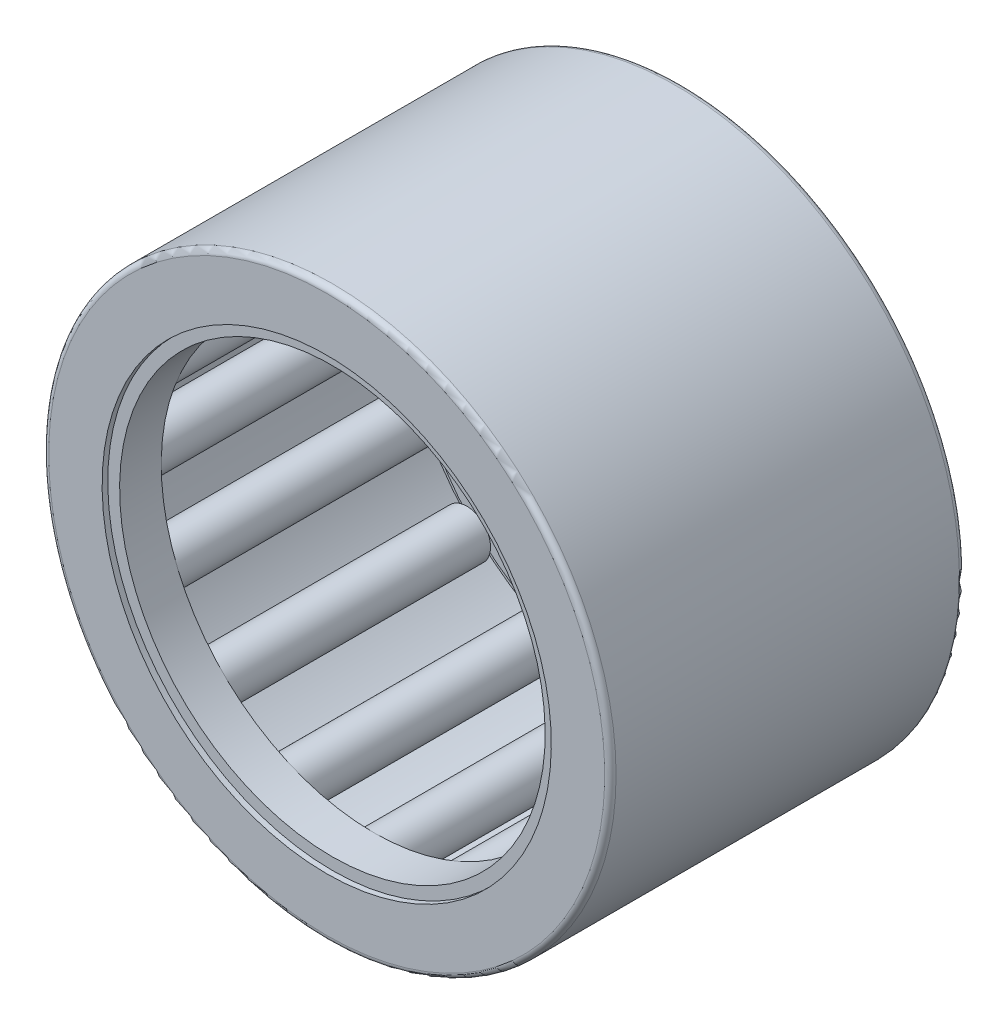
SolidWorks part; units mm, degrees
material "Alloy Steel"
ref_plane "Front Plane" through (0, 0, 0) normal (0, 0, 1) x (1, 0, 0)
ref_plane "Top Plane" through (0, 0, 0) normal (0, 1, 0) x (1, 0, 0)
ref_plane "Right Plane" through (0, 0, 0) normal (1, 0, 0) x (0, 0, -1)
sketch "Sketch1" plane through (0, 0, 0) normal (1, 0, 0) x (0, 0, -1)
  line L0 (-7.9375, 0) -> (7.9375, 0) construction
  line L1 (0, 0) -> (0, 12.7) construction
  line L2 (-7.9375, 0) -> (-7.9375, 12.7) construction
  line L3 (-7.9375, 12.7) -> (7.9375, 12.7)
  line L4 (7.9375, 12.7) -> (7.9375, 0) construction
  line L5 (7.9375, 0) -> (6.8792, 0) construction
  line L6 (6.8792, 0) -> (6.8792, 11.6417) construction
  line L7 (6.8792, 11.6417) -> (-6.8792, 11.6417)
  line L8 (-6.8792, 11.6417) -> (-6.8792, 0) construction
  line L9 (-6.8792, 0) -> (-7.9375, 0) construction
  line L10 (-7.9375, 12.7) -> (-7.9375, 10.0542)
  line L11 (-7.9375, 10.0542) -> (-6.8792, 10.0542)
  line L12 (-6.8792, 10.0542) -> (-6.8792, 11.6417)
  line L13 (6.8792, 12.7) -> (6.8792, 11.6417) construction
  line L14 (6.8792, 11.6417) -> (6.8792, 10.0542)
  line L15 (6.8792, 10.0542) -> (7.9375, 10.0542)
  line L16 (7.9375, 10.0542) -> (7.9375, 12.7)
  line L17 (6.8792, 11.6417) -> (6.8792, 10.5833) construction
  line L18 (6.8792, 10.5833) -> (6.8792, 9.525) construction
  line L19 (6.8792, -11.6417) -> (6.8792, -10.5833) construction
  line L20 (6.8792, -12.7) -> (6.8792, -11.6417) construction
  line L21 (7.9375, -10.0542) -> (7.9375, -12.7) construction
  line L22 (6.8792, -10.0542) -> (7.9375, -10.0542) construction
  line L23 (6.8792, -11.6417) -> (6.8792, -10.0542) construction
  line L24 (-6.8792, -10.0542) -> (-6.8792, -11.6417) construction
  line L25 (-7.9375, -10.0542) -> (-6.8792, -10.0542) construction
  line L26 (-7.9375, -12.7) -> (-7.9375, -10.0542) construction
  line L27 (6.8792, -11.6417) -> (-6.8792, -11.6417) construction
  line L28 (-7.9375, -12.7) -> (7.9375, -12.7) construction
  point P5 (0, 9.525)
  dimension "Width" = 15.875
  dimension "OD" = 25.4
  dimension "Shaft Dia" = 19.05
revolve "Revolve1" add sketch "Sketch1" angle 360 about L0
sketch "Sketch2" plane through (0, 0, 0) normal (1, 0, 0) x (0, 0, -1)
  line L0 (6.8792, 11.6417) -> (-6.8792, 11.6417) construction
  line L1 (-5.8208, 10.5833) -> (5.8208, 10.5833) construction
  line L2 (-5.8208, 10.5833) -> (-5.8208, 11.6417) construction
  line L3 (-5.8208, 11.6417) -> (5.8208, 11.6417)
  line L4 (5.8208, 10.5833) -> (5.8208, 11.6417) construction
  line L5 (6.8792, 10.0542) -> (7.9375, 10.0542) construction
  line L6 (-6.8792, 10.5833) -> (-5.8208, 10.5833) construction
  line L7 (5.8208, 10.5833) -> (6.8792, 10.5833) construction
  line L8 (-7.9375, 10.0542) -> (-6.8792, 10.0542) construction
  line L9 (-5.8208, 10.8479) -> (-5.8208, 10.3188) construction
  line L10 (-6.8792, 10.5833) -> (-6.8792, 10.0542) construction
  line L11 (-5.8208, 11.6417) -> (-5.8208, 10.8479)
  line L12 (5.8208, 11.6417) -> (5.8208, 10.8479)
  line L13 (5.8208, 10.8479) -> (-5.8208, 10.8479)
  line L14 (0, 11.6417) -> (0, 9.525) construction
  line L15 (-6.8792, 10.0542) -> (-6.8792, 11.6417) construction
  line L16 (-5.8208, 10.3188) -> (-6.8792, 10.3188) construction
  line L17 (0, 0) -> (7.9375, 0) construction
  line L18 (-5.8208, -10.3188) -> (-6.8792, -10.3188) construction
  line L19 (0, -11.6417) -> (0, -9.525) construction
  line L20 (-6.8792, -10.5833) -> (-6.8792, -10.0542) construction
  line L21 (-5.8208, -10.8479) -> (-5.8208, -10.3188) construction
  line L22 (5.8208, -10.5833) -> (6.8792, -10.5833) construction
  line L23 (-6.8792, -10.5833) -> (-5.8208, -10.5833) construction
  line L24 (5.8208, -10.5833) -> (5.8208, -11.6417) construction
  line L25 (-5.8208, -10.5833) -> (-5.8208, -11.6417) construction
  line L26 (-5.8208, -10.5833) -> (5.8208, -10.5833) construction
  line L27 (5.8208, -10.8479) -> (-5.8208, -10.8479) construction
  line L28 (5.8208, -11.6417) -> (5.8208, -10.8479) construction
  line L29 (-5.8208, -11.6417) -> (-5.8208, -10.8479) construction
  line L30 (-5.8208, -11.6417) -> (5.8208, -11.6417) construction
  line L31 (7.9375, -12.7) -> (7.9375, 12.7) construction
  point P16 (0, 10.5833)
revolve "Revolve2" add sketch "Sketch2" angle 360 about L1
sketch "Sketch3" plane through (0, 0, 0) normal (1, 0, 0) x (0, 0, -1)
  line L0 (6.8792, 11.6417) -> (6.8792, 10.0542) construction
  line L1 (-6.8792, 10.5833) -> (6.8792, 10.5833)
  line L2 (-6.8792, 10.5833) -> (-6.8792, 10.8479)
  line L3 (-6.8792, 10.8479) -> (6.8792, 10.8479)
  line L4 (6.8792, 10.5833) -> (6.8792, 10.8479)
  line L5 (0, 0) -> (7.9375, 0) construction
  line L6 (7.9375, -12.7) -> (7.9375, 12.7) construction
  line L7 (6.8792, -10.5833) -> (6.8792, -10.8479) construction
  line L8 (-6.8792, -10.8479) -> (6.8792, -10.8479) construction
  line L9 (-6.8792, -10.5833) -> (-6.8792, -10.8479) construction
  line L10 (-6.8792, -10.5833) -> (6.8792, -10.5833) construction
revolve "Revolve3" add sketch "Sketch3" angle 360 about L1
ref_axis "Axis1" through (0, 0, -7.9375) along (0, 0, 1)
pattern_circular "CirPattern1" count 16 every 22.5 about axis through (0, 0, -7.9375) along (0, 0, 1) of bodies 166 167
fillet "Fillet1" radius 0.254 2 edges at (0, -12.7, -7.9375) (0, -12.7, 7.9375)
sketch "Sketch4" plane through (0, 0, 0) normal (1, 0, 0) x (0, 0, -1)
  line L1 (7.6835, 9.525) -> (5.8208, 9.525)
  line L2 (7.6835, 9.525) -> (7.6835, 10.0542)
  line L3 (7.6835, 10.0542) -> (5.8208, 10.0542)
  line L4 (5.8208, 9.525) -> (5.8208, 10.0542)
  line L5 (-7.9375, 10.0542) -> (-6.8792, 10.0542) construction
  line L6 (7.6835, -12.7) -> (7.6835, 12.7) construction
  line L7 (5.8208, 11.6417) -> (5.8208, 10.8479) construction
revolve "Revolve4" add sketch "Sketch4" angle 360 about L0
sketch "Sketch5" plane through (0, 0, 0) normal (1, 0, 0) x (0, 0, -1)
  line L0 (-7.6835, 12.7) -> (-7.6835, -12.7) construction
  line L1 (-5.8208, 9.525) -> (-7.6835, 9.525)
  line L2 (-5.8208, 9.525) -> (-5.8208, 10.0542)
  line L3 (-5.8208, 10.0542) -> (-7.6835, 10.0542)
  line L4 (-7.6835, 9.525) -> (-7.6835, 10.0542)
  line L6 (-5.8208, 11.6417) -> (-5.8208, 10.8479) construction
  line L7 (-7.9375, 10.0542) -> (-6.8792, 10.0542) construction
revolve "Revolve5" add sketch "Sketch5" angle 360 about L0
equation "\"Angle@CirPattern1\" = 360/\"Rollers@CirPattern1\""
equation "\"Rollers@CirPattern1\" = \"OD@Sketch1\"*16"
equation "\"D1@Fillet1\" = \"OD@Sketch1\"*.01"
